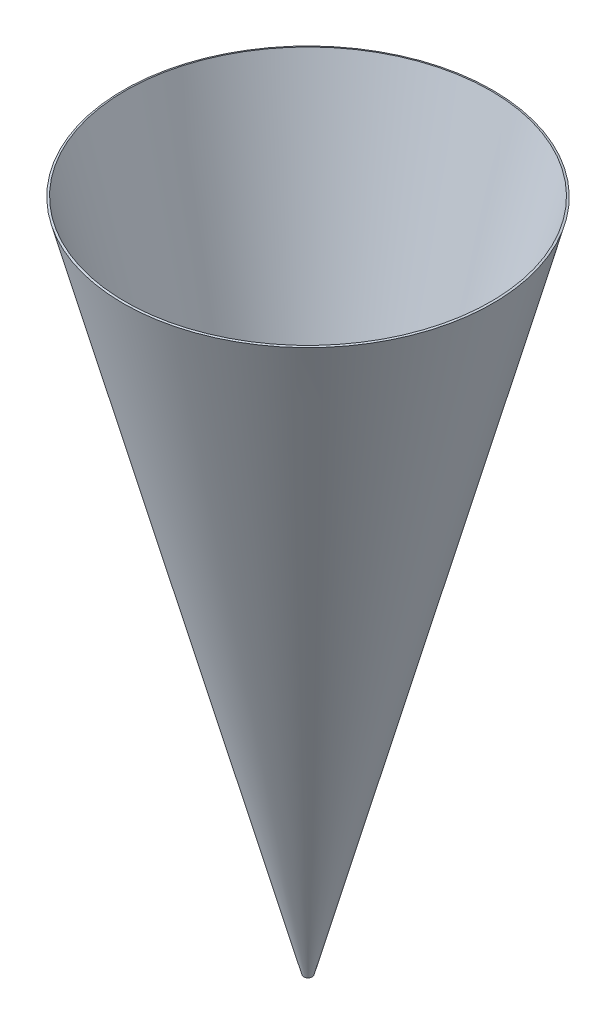
SolidWorks part; units mm, degrees
ref_plane "Front Plane" through (0, 0, 0) normal (0, 0, 1) x (1, 0, 0)
ref_plane "Top Plane" through (0, 0, 0) normal (0, 1, 0) x (1, 0, 0)
ref_plane "Right Plane" through (0, 0, 0) normal (1, 0, 0) x (0, 0, -1)
sketch "Sketch1" plane through (0, 0, 0) normal (0, 0, 1) x (1, 0, 0)
  line L0 (0.0635, 0) -> (2.743, 10)
  line L1 (0, 0) -> (0, 10) construction
  dimension "D1" = 15
  dimension "D2" = 0.0635
  dimension "D3" = 10
revolve "Revolve-Thin1" add sketch "Sketch1" angle 360 about L1 wall 0.03
